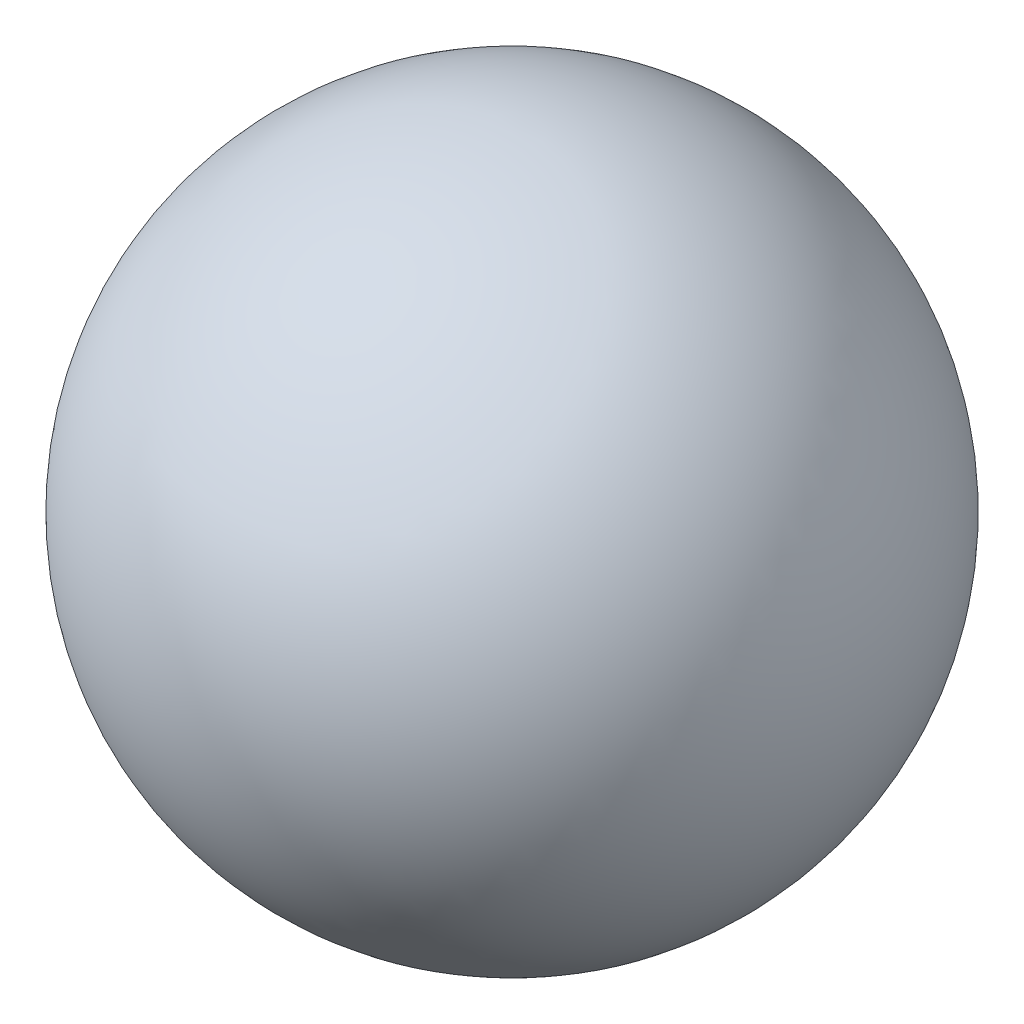
SolidWorks part; units mm, degrees
ref_plane "前视基准面" through (0, 0, 0) normal (0, 0, 1) x (1, 0, 0)
ref_plane "上视基准面" through (0, 0, 0) normal (0, 1, 0) x (1, 0, 0)
ref_plane "右视基准面" through (0, 0, 0) normal (1, 0, 0) x (0, 0, -1)
sketch "草图1" plane through (0, 0, 0) normal (0, 0, 1) x (1, 0, 0)
  line L0 (0, 21.25) -> (0, -21.25)
  arc A0 (0, -21.25) -> (0, 21.25) centre (0, 0) ccw
  dimension "D1" = 42.5
revolve "旋转2" add sketch "草图1" angle 360 about L0
